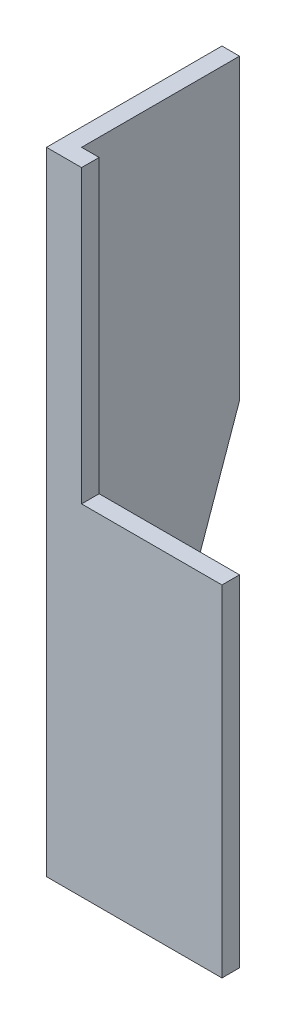
SolidWorks part; units mm, degrees
ref_plane "Alzado" through (0, 0, 0) normal (0, 0, 1) x (1, 0, 0)
ref_plane "Planta" through (0, 0, 0) normal (0, 1, 0) x (1, 0, 0)
ref_plane "Vista lateral" through (0, 0, 0) normal (1, 0, 0) x (0, 0, -1)
sketch "Croquis1" plane through (0, 0, 0) normal (0, 1, 0) x (1, 0, 0)
  line L0 (0, 0) -> (0, 50)
  line L1 (0, 0) -> (50, 0)
  line L2 (5, 5) -> (50, 5)
  line L3 (5, 5) -> (5, 50)
  line L4 (0, 50) -> (5, 50)
  line L5 (50, 5) -> (50, 0)
  dimension "D1" = 50
  dimension "D2" = 5
extrude "Saliente-Extruir1" add sketch "Croquis1" along normal blind 180
sketch "Croquis2" plane through (0, 0, 0) normal (-1, 0, 0) x (0, 0, 1)
  line L0 (-50, 95) -> (0, 95) construction
  line L1 (-50, 180) -> (-50, 0) construction
  line L2 (0, 180) -> (0, 0) construction
  line L3 (-50, 180) -> (0, 180) construction
  line L4 (-50, 95) -> (-16.6667, 0)
  line L5 (-50, 0) -> (0, 0) construction
  line L6 (-16.6667, 0) -> (0, 0)
  line L9 (-50, 95) -> (-50, 0)
  line L10 (-50, 0) -> (-16.6667, 0)
  line M8 (-50, 0) -> (0, 0)
  line M11 (-50, 180) -> (-50, 0)
  dimension "D1" = 85
  dimension "D2" = 16.6667
extrude "Cortar-Extruir1" cut sketch "Croquis2" against normal up to surface (5 mm away) contours L4 M11 M8 up to face at (5, 90, -27.5)
sketch "Croquis3" plane through (0, 0, 0) normal (0, 0, 1) x (1, 0, 0)
  line L0 (0, 180) -> (0, 0) construction
  line L1 (50, 180) -> (10, 180)
  line L2 (50, 180) -> (50, 97)
  line L3 (50, 97) -> (10, 97)
  line L4 (10, 180) -> (10, 97)
  dimension "D1" = 10
  dimension "D2" = 83
extrude "Cortar-Extruir2" cut sketch "Croquis3" against normal up to surface (5 mm away) up to face at (27.5, 90, -5)
